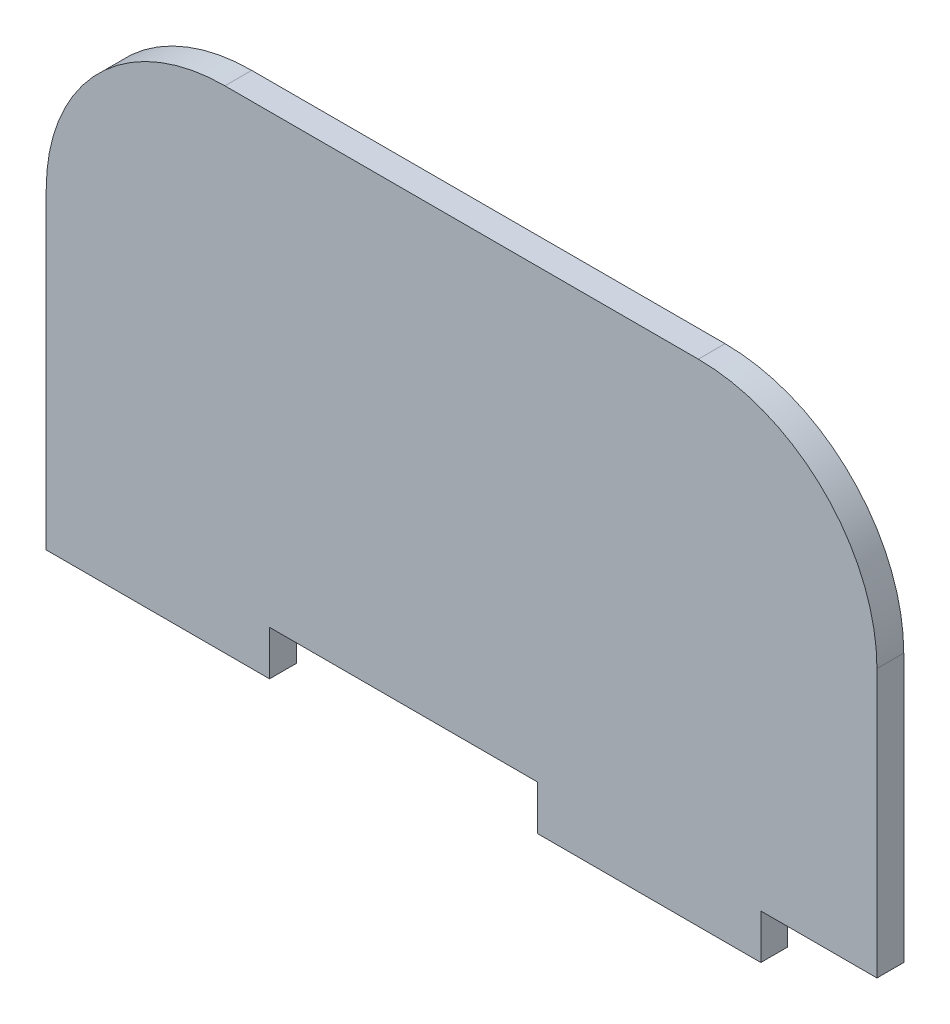
SolidWorks part; units mm, degrees
ref_plane "Plano frontal" through (0, 0, 0) normal (0, 0, 1) x (1, 0, 0)
ref_plane "Plano superior" through (0, 0, 0) normal (0, 1, 0) x (1, 0, 0)
ref_plane "Plano direito" through (0, 0, 0) normal (1, 0, 0) x (0, 0, -1)
sketch "Esboço1" plane through (0, 0, 0) normal (0, 0, 1) x (1, 0, 0)
  line L0 (43.0401, -1.3817) -> (56.0401, -1.3817)
  line L1 (-16.9599, 48.6183) -> (36.0401, 48.6183)
  line L2 (-36.9599, 28.6183) -> (-36.9599, -1.3817)
  line L3 (-11.9599, -1.3817) -> (18.0401, -1.3817)
  line L4 (56.0401, 28.6183) -> (56.0401, -1.3817)
  line L6 (-36.9599, -1.3817) -> (-36.9599, -6.3817)
  line L7 (-36.9599, -6.3817) -> (-11.9599, -6.3817)
  line L8 (-11.9599, -1.3817) -> (-11.9599, -6.3817)
  line L10 (18.0401, -1.3817) -> (18.0401, -6.3817)
  line L11 (18.0401, -6.3817) -> (43.0401, -6.3817)
  line L12 (43.0401, -1.3817) -> (43.0401, -6.3817)
  arc A0 (36.0401, 48.6183) -> (56.0401, 28.6183) centre (36.0401, 28.6183) cw
  arc A1 (-16.9599, 48.6183) -> (-36.9599, 28.6183) centre (-16.9599, 28.6183) ccw
  point P13 (56.0401, 48.6183)
  point P16 (-36.9599, 48.6183)
  dimension "D8" = 20
  dimension "D1" = 93
  dimension "D2" = 5
  dimension "D3" = 25
  dimension "D4" = 30
  dimension "D5" = 25
  dimension "D6" = 5
  dimension "D7" = 50
extrude "Ressalto-extrusão1" add sketch "Esboço1" along normal blind 3
